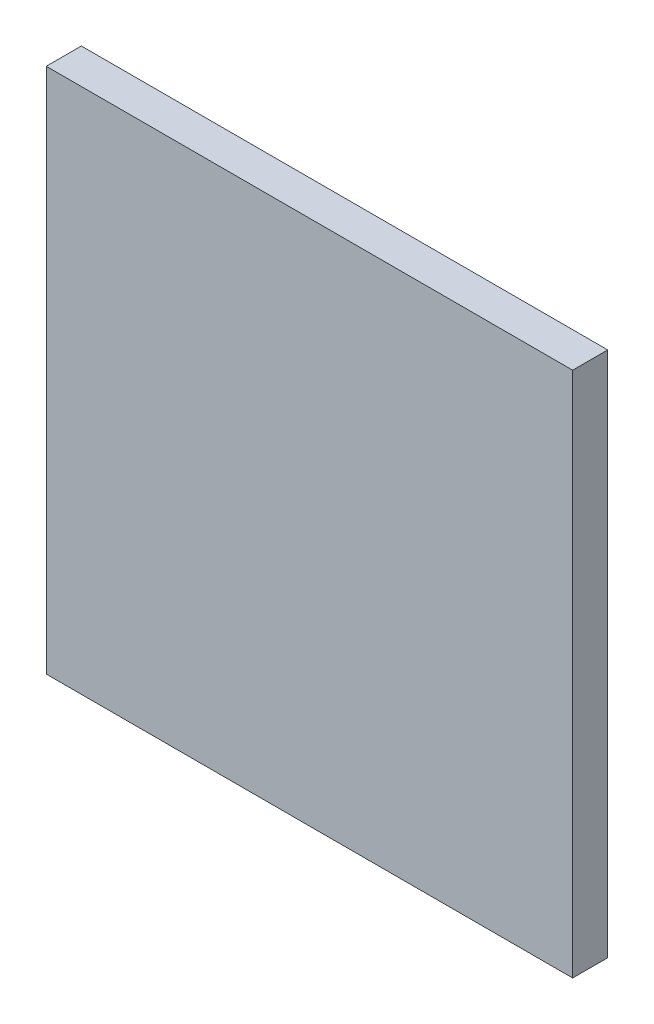
SolidWorks part; units mm, degrees
material "Kayın"
ref_plane "Ön Düzlem" through (0, 0, 0) normal (0, 0, 1) x (1, 0, 0)
ref_plane "Üst Düzlem" through (0, 0, 0) normal (0, 1, 0) x (1, 0, 0)
ref_plane "Sağ Düzlem" through (0, 0, 0) normal (1, 0, 0) x (0, 0, -1)
sketch "Çizim1" plane through (0, 0, 0) normal (0, 0, 1) x (1, 0, 0)
  line L1 (-150, -150) -> (150, -150)
  line L2 (-150, -150) -> (-150, 150)
  line L3 (-150, 150) -> (150, 150)
  line L4 (150, -150) -> (150, 150)
  line L5 (-150, -150) -> (150, 150) construction
  line L6 (-150, 150) -> (150, -150) construction
  point P0 (0, 0)
  dimension "D1" = 300
  dimension "D2" = 300
extrude "Yükseklik-Ekstrüzyon1" add sketch "Çizim1" against normal blind 20
